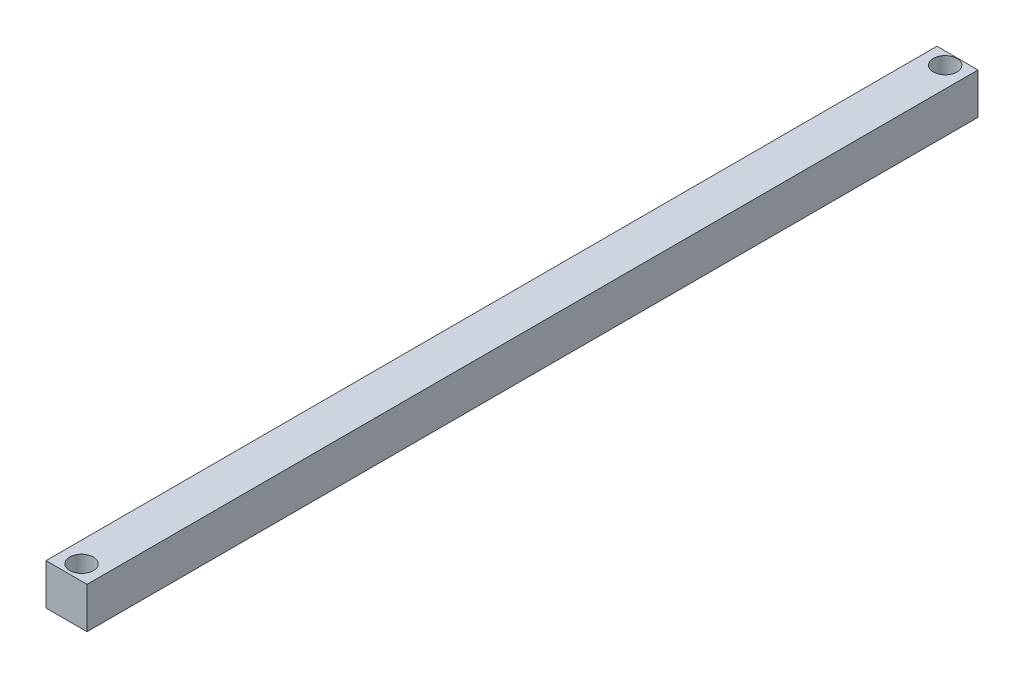
SolidWorks part; units mm, degrees
ref_plane "Front Plane" through (0, 0, 0) normal (0, 0, 1) x (1, 0, 0)
ref_plane "Top Plane" through (0, 0, 0) normal (0, 1, 0) x (1, 0, 0)
ref_plane "Right Plane" through (0, 0, 0) normal (1, 0, 0) x (0, 0, -1)
sketch "Sketch1" plane through (0, 0, 0) normal (0, 1, 0) x (1, 0, 0)
  line L1 (-10, 217) -> (10, 217)
  line L2 (-10, 217) -> (-10, -217)
  line L3 (-10, -217) -> (10, -217)
  line L4 (10, 217) -> (10, -217)
  line L5 (-10, 217) -> (10, -217) construction
  line L6 (-10, -217) -> (10, 217) construction
  point P0 (0, 0)
  dimension "D1" = 20
  dimension "D2" = 434
extrude "Boss-Extrude1" add sketch "Sketch1" along normal blind 20
sketch "Sketch3" plane through (0, 20, 0) normal (0, 1, 0) x (1, 0, 0)
  line L0 (10, 217) -> (-10, 217) construction
  line L1 (10, -217) -> (10, 217) construction
  line L2 (0, 211) -> (0, -209.68) construction
  circle A0 centre (0, 211) radius 5.75
  circle A1 centre (0, -209.68) radius 5.75
  dimension "D1" = 11.5
  dimension "D5" = 11.5
  dimension "D2" = 6
  dimension "D3" = 10
  dimension "D4" = 420.68
extrude "Cut-Extrude1" cut sketch "Sketch3" against normal through all
